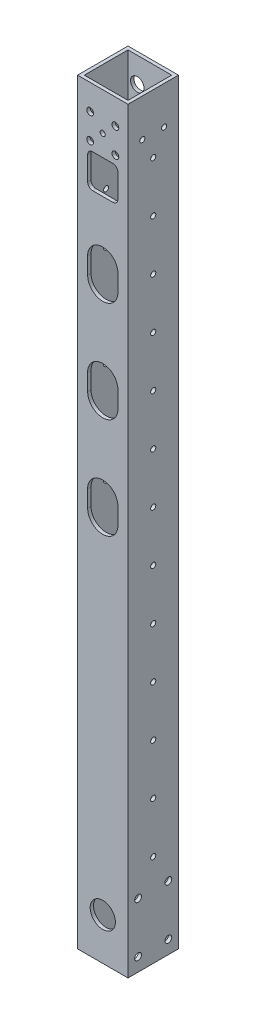
SolidWorks part; units mm, degrees
material "6063-T5"
ref_plane "前视基准面" through (0, 0, 0) normal (0, 0, 1) x (1, 0, 0)
ref_plane "上视基准面" through (0, 0, 0) normal (0, 1, 0) x (1, 0, 0)
ref_plane "右视基准面" through (0, 0, 0) normal (1, 0, 0) x (0, 0, -1)
other "Configuration Table"
sketch "草图2" plane through (0, 0, 0) normal (0, 1, 0) x (1, 0, 0)
  line L1 (-15, -15) -> (15, -15)
  line L2 (-15, -15) -> (-15, 15)
  line L3 (-15, 15) -> (15, 15)
  line L4 (15, -15) -> (15, 15)
  line L5 (-15, -15) -> (15, 15) construction
  line L6 (-15, 15) -> (15, -15) construction
  point P0 (0, 0)
  dimension "D1" = 30
  dimension "D2" = 30
extrude "凸台-拉伸1" add sketch "草图2" along normal mid plane 450
sketch "草图4" plane through (0, 0, 0) normal (0, 1, 0) x (1, 0, 0)
  line L14 (-13, -13) -> (13, -13)
  line L15 (13, -13) -> (13, 13)
  line L16 (-13, 13) -> (-13, -13)
  line L17 (13, 13) -> (-13, 13)
  line L18 (-13, -13) -> (13, -13)
  line L19 (13, -13) -> (13, 13)
  line L20 (-13, 13) -> (-13, -13)
  line L21 (13, 13) -> (-13, 13)
  dimension "D1" = 2
extrude "切除-拉伸1" cut sketch "草图4" against normal through all both and the other way through all
sketch "草图5" plane through (0, 0, -15) normal (0, 0, -1) x (-1, 0, 0)
  circle A0 centre (-7.5, 210) radius 2.025
  circle A1 centre (7.5, 210) radius 2.025
  circle A2 centre (-7.5, 195) radius 2.025
  circle A3 centre (7.5, 195) radius 2.025
  circle A8 centre (7.5, 210) radius 1.65 construction
  circle A9 centre (-7.5, 210) radius 1.65 construction
  circle A10 centre (7.5, 195) radius 1.65 construction
  circle A11 centre (-7.5, 195) radius 1.65 construction
  dimension "D1" = 4.05
extrude "切除-拉伸2" cut sketch "草图5" against normal through all both and the other way through all
sketch "草图6" plane through (0, 0, -15) normal (0, 0, -1) x (-1, 0, 0)
  circle A0 centre (-7.5, 210) radius 4
  circle A1 centre (-7.5, 195) radius 4
  circle A2 centre (7.5, 195) radius 4
  circle A3 centre (7.5, 210) radius 4
  circle A4 centre (-7.5, 195) radius 2.025 construction
  dimension "D1" = 8
sketch "草图7" plane through (0, 0, -15) normal (0, 0, -1) x (-1, 0, 0)
  line L6 (0, -196.5) -> (0, -165.5) construction
  line L7 (-9, -196.5) -> (-9, -165.5)
  line L8 (9, -196.5) -> (9, -165.5)
  line L9 (-15, -225) -> (15, -225) construction
  arc A0 (-9, -196.5) -> (9, -196.5) centre (0, -196.5) ccw
  arc A1 (9, -165.5) -> (-9, -165.5) centre (0, -165.5) ccw
  point P2 (0, -181)
  dimension "D1" = 18
  dimension "D2" = 31
  dimension "D3" = 44
extrude "切除-拉伸3" cut sketch "草图7" against normal blind 10
sketch "草图8" plane through (15, 0, 0) normal (1, 0, 0) x (0, 0, -1)
  circle A0 centre (0, -170) radius 1.525
  dimension "D1" = 3.05
extrude "切除-拉伸4" cut sketch "草图8" against normal through all both and the other way through all
pattern_linear "阵列(线性)2" count 13 spacing 30 along (0, 1, 0) of "切除-拉伸4"
pattern_linear "阵列(线性)3" count 7 spacing 57 along (0, 1, 0) of "切除-拉伸3"
sketch "草图9" plane through (15, 0, 0) normal (1, 0, 0) x (0, 0, -1)
  circle A0 centre (6.5, 202.5) radius 1.525
  circle A1 centre (-6.5, 202.5) radius 1.525
  dimension "D1" = 3.05
  dimension "D2" = 3.05
extrude "切除-拉伸5" cut sketch "草图9" against normal through all both and the other way through all
sketch "草图10" plane through (15, 0, 0) normal (1, 0, 0) x (0, 0, -1)
  line L0 (15, 225) -> (15, -225) construction
  line L1 (-9, -187) -> (9, -187) construction
  line L2 (-9, -187) -> (-9, -217) construction
  line L3 (-9, -217) -> (9, -217) construction
  line L4 (9, -187) -> (9, -217) construction
  line L5 (-15, -225) -> (15, -225) construction
  circle A0 centre (9, -187) radius 2.025
  circle A1 centre (-9, -187) radius 2.025
  circle A2 centre (-9, -217) radius 2.025
  circle A3 centre (9, -217) radius 2.025
  dimension "D1" = 4.05
  dimension "D2" = 30
  dimension "D3" = 18
  dimension "D4" = 6
  dimension "D5" = 8
extrude "切除-拉伸6" cut sketch "草图10" against normal through all both
extrude "切除-拉伸7" cut sketch "草图6" against normal blind 10
sketch "草图11" plane through (0, 0, 15) normal (0, 0, 1) x (1, 0, 0)
  line L0 (0, 125) -> (0, 135) construction
  line L1 (-9, 125) -> (-9, 135)
  line L2 (9, 125) -> (9, 135)
  line L3 (0, 65) -> (0, 75) construction
  line L4 (-9, 65) -> (-9, 75)
  line L5 (9, 65) -> (9, 75)
  line L6 (0, 5) -> (0, 15) construction
  line L7 (-9, 5) -> (-9, 15)
  line L8 (9, 5) -> (9, 15)
  arc A0 (-9, 125) -> (9, 125) centre (0, 125) ccw
  arc A1 (9, 135) -> (-9, 135) centre (0, 135) ccw
  arc A2 (-9, 65) -> (9, 65) centre (0, 65) ccw
  arc A3 (9, 75) -> (-9, 75) centre (0, 75) ccw
  arc A4 (-9, 5) -> (9, 5) centre (0, 5) ccw
  arc A5 (9, 15) -> (-9, 15) centre (0, 15) ccw
  point P2 (0, 130)
  point P7 (0, 70)
  point P14 (0, 10)
  point P15 (9, 70)
  point P17 (9, 130)
  point P24 (9, 10)
  dimension "D4" = 9
  dimension "D1" = 70
  dimension "D2" = 130
  dimension "D3" = 10
  dimension "D5" = 10
extrude "切除-拉伸8" cut sketch "草图11" against normal blind 10
sketch "草图12" plane through (0, 0, 15) normal (0, 0, 1) x (1, 0, 0)
  line L0 (-15, 225) -> (15, 225) construction
  line L1 (-6, 170) -> (6, 170)
  line L2 (-9, 173) -> (-9, 187)
  line L3 (-6, 190) -> (6, 190)
  line L4 (9, 173) -> (9, 187)
  line L5 (-9, 170) -> (9, 190) construction
  line L6 (-9, 190) -> (9, 170) construction
  arc A0 (6, 190) -> (9, 187) centre (6, 187) cw
  arc A1 (6, 170) -> (9, 173) centre (6, 173) ccw
  arc A2 (-6, 170) -> (-9, 173) centre (-6, 173) cw
  arc A3 (-9, 187) -> (-6, 190) centre (-6, 187) cw
  point P0 (0, 180)
  dimension "D4" = 3
  dimension "D1" = 18
  dimension "D2" = 20
  dimension "D3" = 35
extrude "切除-拉伸9" cut sketch "草图12" against normal blind 10
sketch "草图13" plane through (0, 0, -15) normal (0, 0, -1) x (-1, 0, 0)
  line L0 (15, 225) -> (15, -225) construction
  line L1 (-15, 225) -> (15, 225) construction
  circle A0 centre (0.05, 202.5) radius 1.525
  dimension "D1" = 3.05
  dimension "D2" = 14.95
  dimension "D3" = 22.5
extrude "切除-拉伸10" cut sketch "草图13" against normal through all both and the other way through all
sketch "草图14" plane through (0, 0, 13) normal (0, 0, -1) x (-1, 0, 0)
  line L0 (-15, -225) -> (15, -225) construction
  circle A0 centre (0, -200) radius 7.5
  point P5 (0, -225)
  dimension "D1" = 15
  dimension "D2" = 25
extrude "切除-拉伸11" cut sketch "草图14" against normal up to surface (2 mm away) up to face at (-1.575, 202.5, 15)
